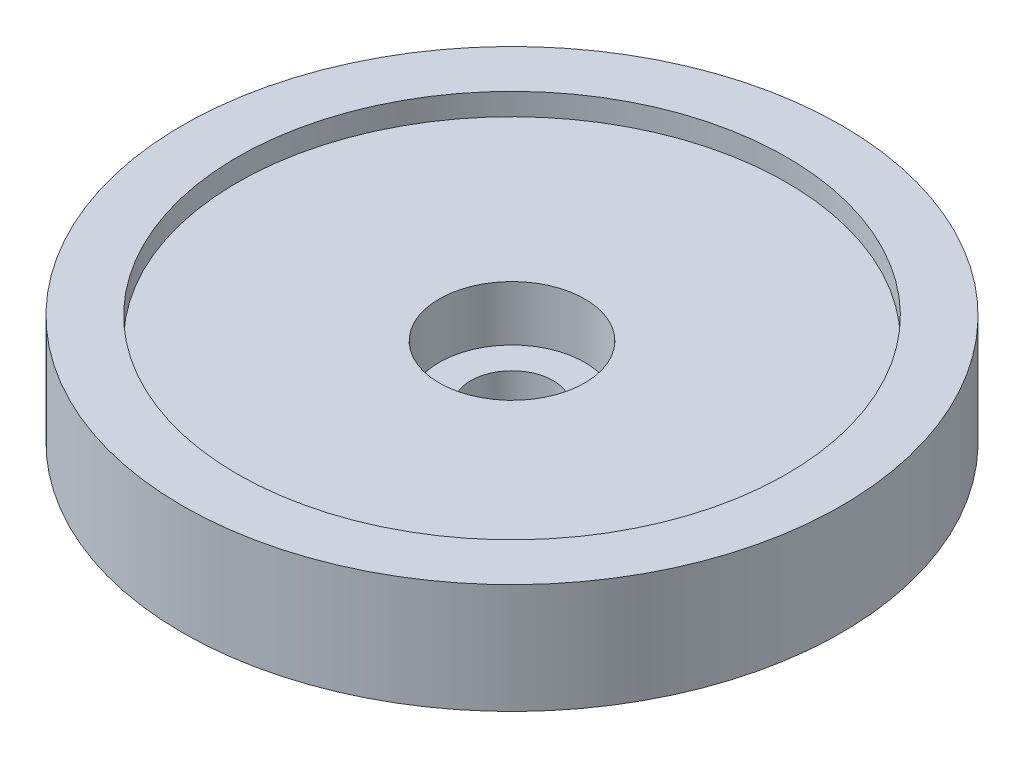
SolidWorks part; units mm, degrees
ref_plane "Front Plane" through (0, 0, 0) normal (0, 0, 1) x (1, 0, 0)
ref_plane "Top Plane" through (0, 0, 0) normal (0, 1, 0) x (1, 0, 0)
ref_plane "Right Plane" through (0, 0, 0) normal (1, 0, 0) x (0, 0, -1)
sketch "Sketch1" plane through (0, 0, 0) normal (0, 1, 0) x (1, 0, 0)
  line L0 (-391.1409, 0) -> (19165.9026, 0) construction
  line L1 (0, -391.1409) -> (0, 19165.9026) construction
  circle A0 centre (0, 0) radius 30
  dimension "D1" = 60
extrude "Boss-Extrude1" add sketch "Sketch1" along normal blind 10
sketch "Sketch2" plane through (0, 10, 0) normal (0, 1, 0) x (1, 0, 0)
  circle A0 centre (0, 0) radius 25
  dimension "D1" = 50
extrude "Cut-Extrude1" cut sketch "Sketch2" against normal blind 2
sketch "Sketch3" plane through (0, 8, 0) normal (0, 1, 0) x (1, 0, 0)
  circle A0 centre (0, 0) radius 6.625
  dimension "D1" = 13.25
extrude "Cut-Extrude2" cut sketch "Sketch3" against normal blind 5
sketch "Sketch4" plane through (0, 3, 0) normal (0, 1, 0) x (1, 0, 0)
  circle A0 centre (0, 0) radius 3.75
  dimension "D1" = 7.5
extrude "Cut-Extrude4" cut sketch "Sketch4" against normal through all both and the other way through all
